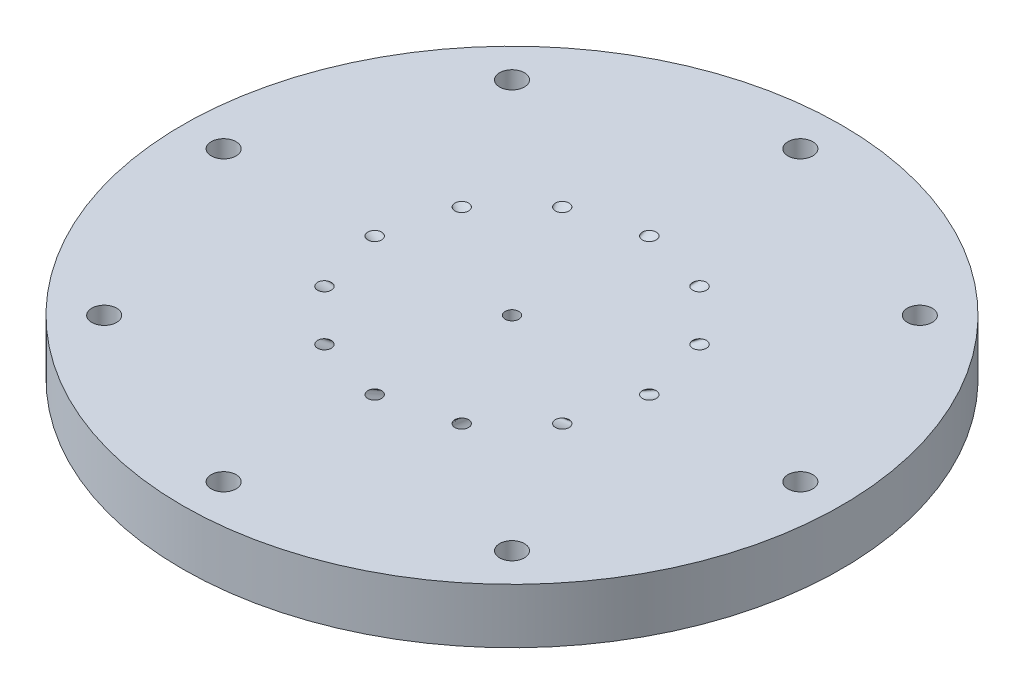
SolidWorks part; units mm, degrees
ref_plane "Front Plane" through (0, 0, 0) normal (0, 0, 1) x (1, 0, 0)
ref_plane "Top Plane" through (0, 0, 0) normal (0, 1, 0) x (1, 0, 0)
ref_plane "Right Plane" through (0, 0, 0) normal (1, 0, 0) x (0, 0, -1)
sketch "Sketch1" plane through (0, 0, 0) normal (0, 1, 0) x (1, 0, 0)
  circle A0 centre (0, 0) radius 38.1
  dimension "D1" = 76.2
extrude "Boss-Extrude1" add sketch "Sketch1" along normal blind 6.35
sketch "Sketch2" plane through (0, 0, 0) normal (0, -1, 0) x (1, 0, 0)
  circle A0 centre (0, 0) radius 33.3375
  circle A1 centre (0, 33.3375) radius 0.762
  dimension "D1" = 66.675
hole_wizard "CBORE for #4 Button Head Cap Screw1" positions "Sketch5" profile "Sketch4" counterbore size "#4" standard "ANSI Inch" end condition through all
sketch "Sketch5" plane through (0, 0, 0) normal (0, -1, 0) x (-1, 0, 0)
  point P0 (0, -33.3375)
sketch "Sketch4" plane through (0, 0, 33.3375) normal (1, 0, 0) x (0, 0, -1)
  line L0 (0, 0) -> (0, 6.35)
  line L1 (0, 6.35) -> (1.4351, 6.35)
  line L3 (1.4351, 6.35) -> (1.4351, 1.905)
  line L4 (1.4351, 1.905) -> (2.413, 1.905)
  line L5 (2.413, 1.905) -> (2.413, 0)
  line L7 (2.413, 0) -> (0, 0)
  line L11 (0, -6.35) -> (0, 107.95) construction
  dimension "Thru Hole Dia." = 2.8702
  dimension "Thru Hole Depth" = 6.35
  dimension "C'Bore Dia." = 4.826
  dimension "C'Bore Depth" = 1.905
pattern_circular "CirPattern1" count 8 over 360 about axis through (0, 0, 0) along (0, 1, 0) of "CBORE for #4 Button Head Cap Screw1"
sketch "Sketch6" plane through (0, 6.35, 0) normal (0, 1, 0) x (1, 0, 0)
  circle A0 centre (0, 0) radius 0.7937
  dimension "D1" = 1.5875
extrude "Cut-Extrude1" cut sketch "Sketch6" against normal through all both and the other way through all
sketch "Sketch7" plane through (0, 6.35, 0) normal (0, 1, 0) x (1, 0, 0)
  circle A0 centre (0, 15.875) radius 0.7937
  circle A1 centre (0, 0) radius 0.7937 construction
  dimension "D1" = 1.5875
  dimension "D2" = 15.875
sketch "Sketch8" plane through (0, 0, 0) normal (0, -1, 0) x (1, 0, 0)
  circle A0 centre (0, -4.445) radius 0.7938
  circle A1 centre (0, 0) radius 0.7937 construction
  dimension "D1" = 1.5875
  dimension "D2" = 4.445
sketch3d "3DSketch1"
  line L0 (0, 6.35, -15.875) -> (0, 0, -4.445)
sweep "Cut-Sweep1" cut profiles "Sketch7" path "3DSketch1"
pattern_circular "CirPattern2" count 12 over 360 about axis through (0, 6.35, 0) along (0, 1, 0) of "Cut-Sweep1"
